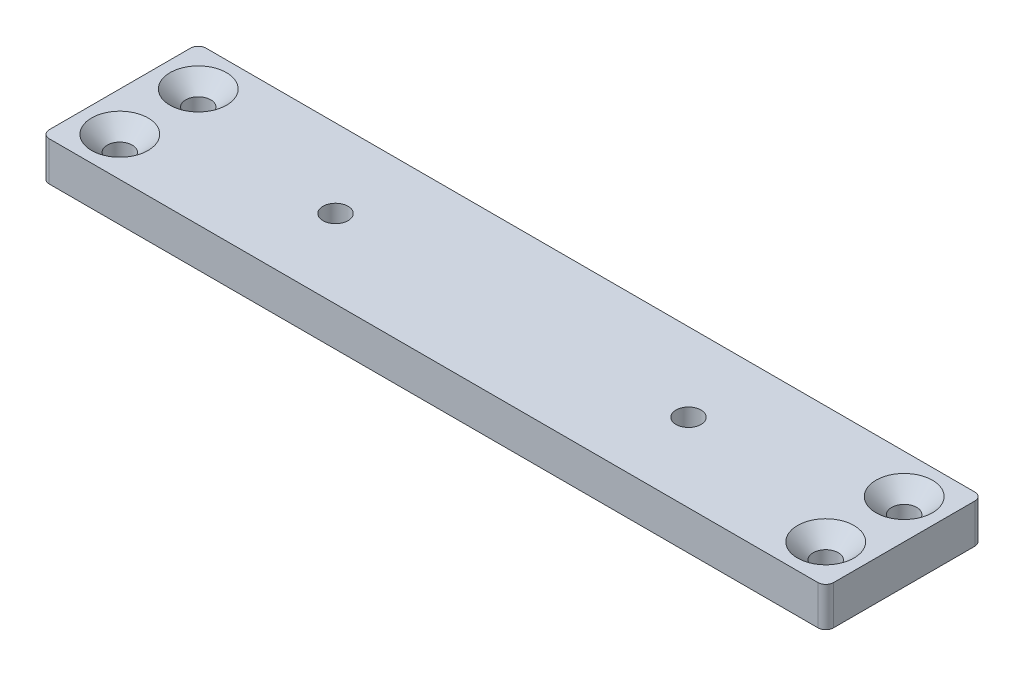
SolidWorks part; units mm, degrees
ref_plane "Plan de face" through (0, 0, 0) normal (0, 0, 1) x (1, 0, 0)
ref_plane "Plan de dessus" through (0, 0, 0) normal (0, 1, 0) x (1, 0, 0)
ref_plane "Plan de droite" through (0, 0, 0) normal (1, 0, 0) x (0, 0, -1)
ref_plane "Plan1" through (0, 5, 0) normal (0, 1, 0) x (1, 0, 0)
sketch "Esquisse1" plane through (0, 5, 0) normal (0, 1, 0) x (1, 0, 0)
  line L0 (50, -20) -> (50, 0)
  line L1 (50, 0) -> (-50, 0)
  line L2 (-50, 0) -> (-50, -20)
  line L3 (-50, -20) -> (50, -20)
extrude "Boss.-Extru.1" add sketch "Esquisse1" against normal blind 5
hole_wizard "Diamètre du perçage Ø3.2 (3.2)1" positions "Esquisse3" profile "Esquisse2" hole size "Ø3.2" standard "Ansi Metric" end condition through all
sketch "Esquisse3" plane through (0, 5, 0) normal (0, 1, 0) x (1, 0, 0)
  point P0 (22.5, -10)
  point P1 (-22.5, -10)
sketch "Esquisse2" plane through (22.5, 5, 10) normal (1, 0, 0) x (0, 0, 1)
  line L0 (0, 0) -> (0, 5)
  line L1 (0, 5) -> (1.6, 5)
  line L2 (1.6, 5) -> (1.6, 0)
  line L5 (1.6, 0) -> (0, 0)
  line L11 (0, -6.35) -> (0, 107.95) construction
  dimension "Diamètre du perçage jusqu'au prochain" = 3.2
  dimension "Profondeur du perçage jusqu'au prochain" = 5
hole_wizard "Diamètre du perçage Ø3.2 (3.2)2" positions "Esquisse5" profile "Esquisse4" hole size "Ø3.2" standard "Ansi Metric" end condition through all
sketch "Esquisse5" plane through (0, 0, 0) normal (0, -1, 0) x (-1, 0, 0)
  line L0 (50, -20) -> (-50, -20) construction
  line L1 (-50, -20) -> (-50, 0) construction
  point P0 (45, -15)
  point P1 (45, -5)
  point P2 (-45, -5)
  point P3 (-45, -15)
  dimension "D1" = 5
  dimension "D2" = 5
  dimension "D3" = 10
sketch "Esquisse4" plane through (-45, 0, 15) normal (1, 0, 0) x (0, 0, -1)
  line L0 (0, 0) -> (0, 5)
  line L1 (0, 5) -> (1.6, 5)
  line L2 (1.6, 5) -> (1.6, 0)
  line L5 (1.6, 0) -> (0, 0)
  line L11 (0, -6.35) -> (0, 107.95) construction
  dimension "Diamètre du perçage jusqu'au prochain" = 3.2
  dimension "Profondeur du perçage jusqu'au prochain" = 5
fillet "Congé1" radius 1 4 edges at (50, 2.5, 0) (-50, 2.5, 20) (50, 2.5, 20) (-50, 2.5, 0)
chamfer "Chanfrein1" distance 2 angle 45 4 edges at (-45, 5, 3.4) (-45, 5, 13.4) (45, 5, 3.4) (45, 5, 13.4)
chamfer "Chanfrein2" distance 2 angle 45 2 edges at (22.5, 0, 11.6) (-22.5, 0, 11.6)
